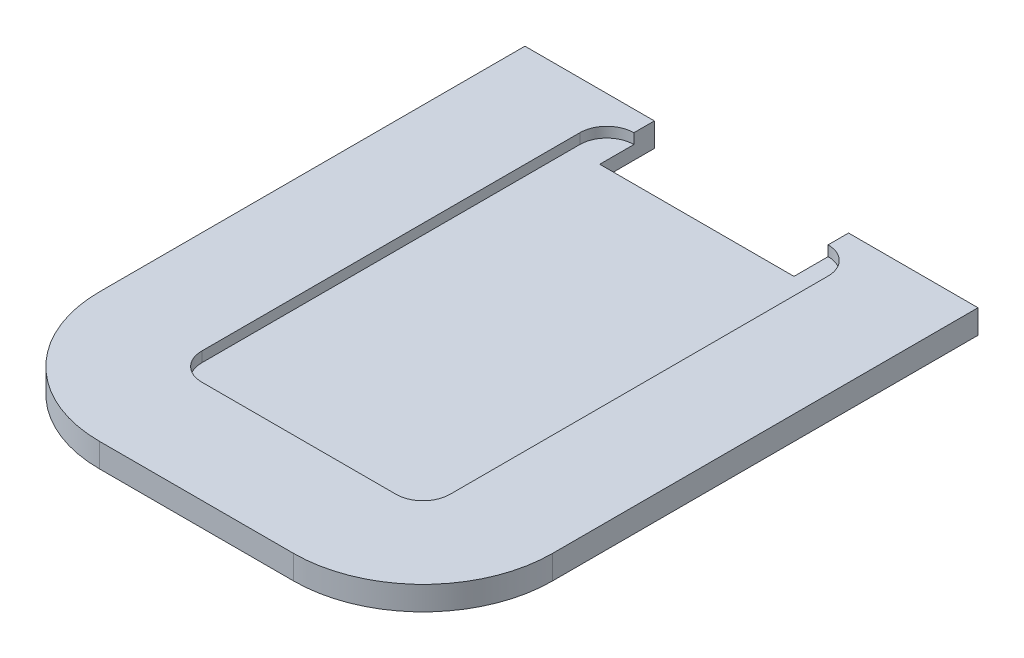
SolidWorks part; units mm, degrees
material "PET"
ref_plane "Front Plane" through (0, 0, 0) normal (0, 0, 1) x (1, 0, 0)
ref_plane "Top Plane" through (0, 0, 0) normal (0, 1, 0) x (1, 0, 0)
ref_plane "Right Plane" through (0, 0, 0) normal (1, 0, 0) x (0, 0, -1)
sketch "Sketch1" plane through (0, 30.4273, 0) normal (0, -1, 0) x (1, 0, 0)
  line L5 (61.676, 19.1563) -> (61.676, 74.5283)
  line L6 (42.716, 93.4883) -> (14.268, 93.4883)
  line L7 (-4.692, 74.5283) -> (-4.692, 19.1563)
  line L16 (-4.2738, 15.1963) -> (61.2579, 15.1963)
  line L17 (-4.692, 19.1563) -> (-4.692, 15.1963)
  line L19 (14.268, 15.1963) -> (42.716, 15.1963)
  line L20 (14.268, 15.1963) -> (14.268, 20.1963)
  line L21 (14.268, 20.1963) -> (42.716, 20.1963)
  line L22 (42.716, 15.1963) -> (42.716, 20.1963)
  line L23 (-4.692, 15.1963) -> (-4.2738, 15.1963)
  line L24 (61.676, 19.1563) -> (61.676, 15.1963)
  line L25 (61.676, 15.1963) -> (61.2579, 15.1963)
  arc A6 (61.676, 74.5283) -> (42.716, 93.4883) centre (42.716, 74.5283) ccw
  arc A7 (14.268, 93.4883) -> (-4.692, 74.5283) centre (14.268, 74.5283) ccw
  point P16 (28.492, 15.1963)
extrude "Boss-Extrude1" add sketch "Sketch1" along normal blind 2
sketch "Sketch3" plane through (0, 30.4273, 0) normal (0, 1, 0) x (1, 0, 0)
  line L8 (10.308, -19.1563) -> (10.308, -74.5283)
  line L9 (14.268, -78.4883) -> (42.716, -78.4883)
  line L10 (46.676, -74.5283) -> (46.676, -19.1563)
  line L11 (42.716, -15.1963) -> (14.268, -15.1963)
  line L12 (10.308, -19.1563) -> (10.308, -74.5283)
  line L13 (14.268, -78.4883) -> (42.716, -78.4883)
  line L14 (46.676, -74.5283) -> (46.676, -19.1563)
  line L15 (42.716, -15.1963) -> (14.268, -15.1963)
  line L28 (14.268, -20.1963) -> (14.268, -15.1963)
  line L29 (14.268, -15.1963) -> (-4.692, -15.1963)
  line L30 (-4.692, -15.1963) -> (-4.692, -74.5283)
  line L31 (14.268, -93.4883) -> (42.716, -93.4883)
  line L32 (61.676, -74.5283) -> (61.676, -15.1963)
  line L33 (61.676, -15.1963) -> (42.716, -15.1963)
  line L34 (42.716, -15.1963) -> (42.716, -20.1963)
  line L35 (42.716, -20.1963) -> (14.268, -20.1963)
  line L36 (14.268, -20.1963) -> (14.268, -15.1963)
  line L37 (14.268, -15.1963) -> (-4.692, -15.1963)
  line L38 (-4.692, -15.1963) -> (-4.692, -74.5283)
  line L39 (14.268, -93.4883) -> (42.716, -93.4883)
  line L40 (61.676, -74.5283) -> (61.676, -15.1963)
  line L41 (61.676, -15.1963) -> (42.716, -15.1963)
  line L42 (42.716, -15.1963) -> (42.716, -20.1963)
  line L43 (42.716, -20.1963) -> (14.268, -20.1963)
  arc A8 (14.268, -15.1963) -> (10.308, -19.1563) centre (14.268, -19.1563) ccw
  arc A9 (10.308, -74.5283) -> (14.268, -78.4883) centre (14.268, -74.5283) ccw
  arc A10 (42.716, -78.4883) -> (46.676, -74.5283) centre (42.716, -74.5283) ccw
  arc A11 (46.676, -19.1563) -> (42.716, -15.1963) centre (42.716, -19.1563) ccw
  arc A12 (14.268, -15.1963) -> (10.308, -19.1563) centre (14.268, -19.1563) ccw
  arc A13 (10.308, -74.5283) -> (14.268, -78.4883) centre (14.268, -74.5283) ccw
  arc A14 (42.716, -78.4883) -> (46.676, -74.5283) centre (42.716, -74.5283) ccw
  arc A15 (46.676, -19.1563) -> (42.716, -15.1963) centre (42.716, -19.1563) ccw
  arc A16 (-4.692, -74.5283) -> (14.268, -93.4883) centre (14.268, -74.5283) ccw
  arc A17 (42.716, -93.4883) -> (61.676, -74.5283) centre (42.716, -74.5283) ccw
  arc A18 (-4.692, -74.5283) -> (14.268, -93.4883) centre (14.268, -74.5283) ccw
  arc A19 (42.716, -93.4883) -> (61.676, -74.5283) centre (42.716, -74.5283) ccw
  line M20 (14.268, -15.1963) -> (-4.692, -15.1963)
  line M21 (-4.692, -15.1963) -> (-4.692, -74.5283)
  arc M22 (-4.692, -74.5283) -> (14.268, -93.4883) centre (14.268, -74.5283) ccw
  line M23 (14.268, -93.4883) -> (42.716, -93.4883)
  arc M24 (42.716, -93.4883) -> (61.676, -74.5283) centre (42.716, -74.5283) ccw
  line M25 (61.676, -74.5283) -> (61.676, -15.1963)
  line M26 (61.676, -15.1963) -> (42.716, -15.1963)
  dimension "D1" = 0.15
  dimension "D2" = 0
extrude "Boss-Extrude4" add sketch "Sketch3" along normal blind 1.5 contours A15 L14 A14 L13 A13 L12 A12 M20 M21 M22 M23 M24 M25 M26
sketch "Sketch4" plane through (0, 28.4273, 0) normal (0, -1, 0) x (1, 0, 0)
  line L0 (14.268, 15.1963) -> (14.268, 20.1963) construction
  line L1 (-4.692, 15.1963) -> (14.268, 15.1963)
  line L2 (-4.692, 15.1963) -> (-4.692, 12.1963)
  line L3 (-4.692, 12.1963) -> (14.268, 12.1963)
  line L4 (14.268, 15.1963) -> (14.268, 12.1963)
  line L5 (61.676, 74.5283) -> (61.676, 15.1963) construction
  line L6 (42.716, 15.1963) -> (61.676, 15.1963)
  line L7 (42.716, 15.1963) -> (42.716, 12.1963)
  line L8 (42.716, 12.1963) -> (61.676, 12.1963)
  line L9 (61.676, 15.1963) -> (61.676, 12.1963)
  dimension "D1" = 0
  dimension "D2" = 3
  dimension "D3" = 0
  dimension "D4" = 3
extrude "Boss-Extrude5" add sketch "Sketch4" against normal blind 3.5
